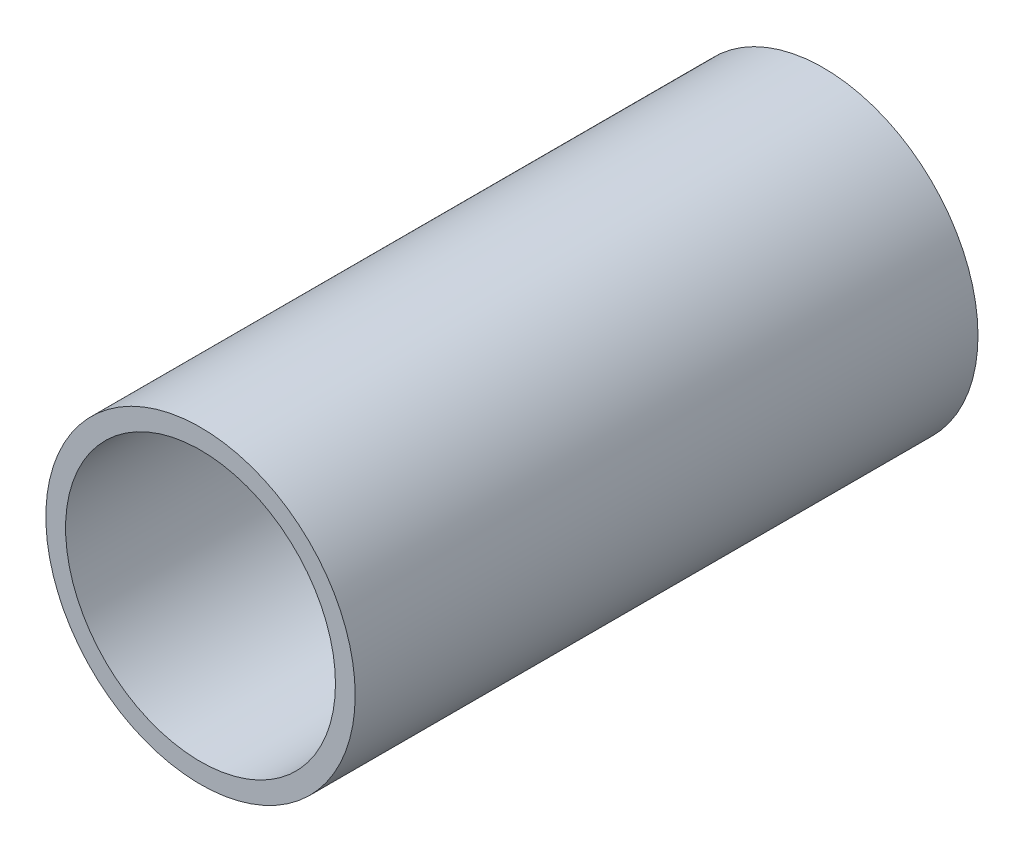
SolidWorks part; units mm, degrees
material "PVC Rigid"
ref_plane "Front Plane" through (0, 0, 0) normal (0, 0, 1) x (1, 0, 0)
ref_plane "Top Plane" through (0, 0, 0) normal (0, 1, 0) x (1, 0, 0)
ref_plane "Right Plane" through (0, 0, 0) normal (1, 0, 0) x (0, 0, -1)
sketch "Sketch1" plane through (0, 0, 0) normal (0, 0, 1) x (1, 0, 0)
  circle A0 centre (0, 0) radius 18.923
  circle A1 centre (0, 0) radius 16.51
  dimension "D1" = 37.846
  dimension "D2" = 33.02
extrude "Boss-Extrude1" add sketch "Sketch1" along normal blind 76.2
